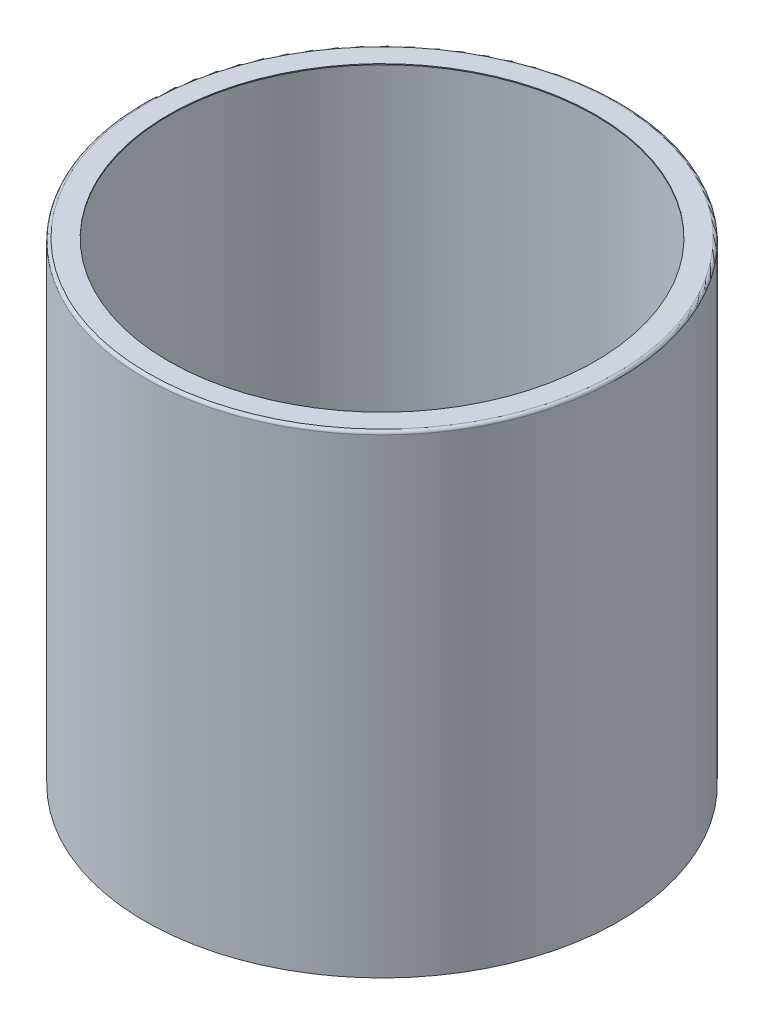
SolidWorks part; units mm, degrees
ref_plane "Front Plane" through (0, 0, 0) normal (0, 0, 1) x (1, 0, 0)
ref_plane "Top Plane" through (0, 0, 0) normal (0, 1, 0) x (1, 0, 0)
ref_plane "Right Plane" through (0, 0, 0) normal (1, 0, 0) x (0, 0, -1)
sketch "Sketch8" plane through (0, 0, 0) normal (1, 0, 0) x (0, 0, -1)
  line L0 (0, 0) -> (254, 0) construction
  line L1 (254, 0) -> (254, -254)
  line L2 (254, -254) -> (255.0287, -254)
  line L3 (255.0287, -254) -> (255.0287, 251.8537)
  line L4 (251.8537, 255.0287) -> (229.6287, 255.0287)
  line L5 (229.6287, 255.0287) -> (229.6287, 254)
  line L6 (229.6287, 254) -> (250.825, 254)
  line L7 (254, 250.825) -> (254, 0)
  line L8 (0, 0) -> (0, 268.6325) construction
  arc A0 (255.0287, 251.8537) -> (251.8537, 255.0287) centre (251.8537, 251.8537) ccw
  arc A1 (254, 250.825) -> (250.825, 254) centre (250.825, 250.825) ccw
  point P11 (255.0287, 255.0287)
  point P14 (254, 254)
  dimension "D7" = 3.175
  dimension "D1" = 254
  dimension "D2" = 254
  dimension "D3" = 254
  dimension "D4" = 25.4
  dimension "D5" = 1.0287
  dimension "D6" = 1.0287
revolve "Revolve1" add sketch "Sketch8" angle 360 about L8
